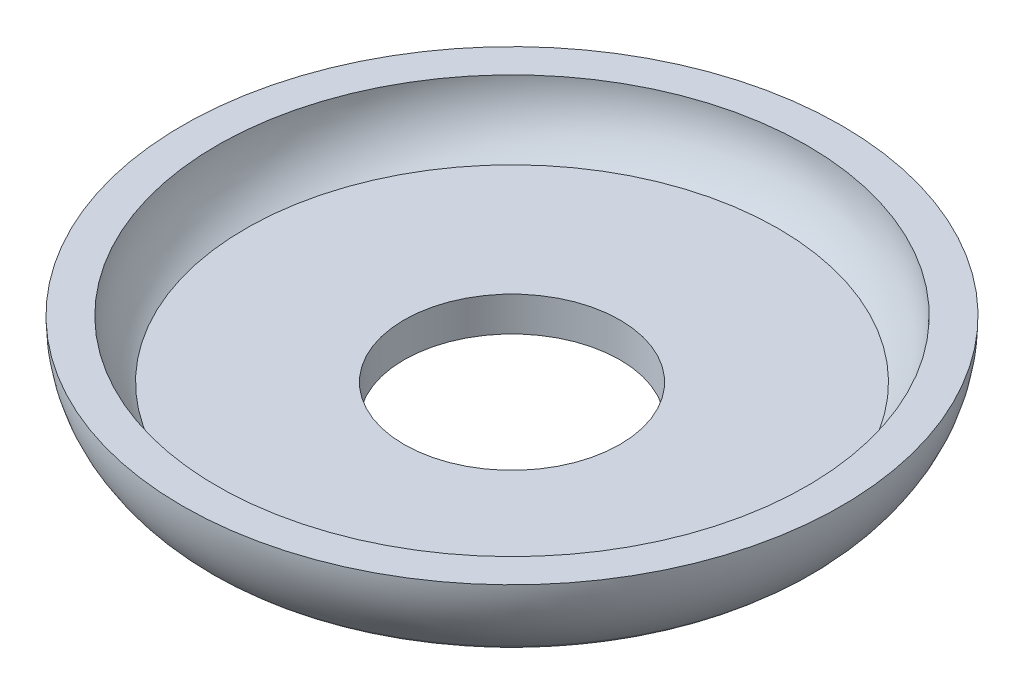
SolidWorks part; units mm, degrees
material "Cast Carbon Steel"
ref_plane "Front" through (0, 0, 0) normal (0, 0, 1) x (1, 0, 0)
ref_plane "Top" through (0, 0, 0) normal (0, 1, 0) x (1, 0, 0)
ref_plane "Right" through (0, 0, 0) normal (1, 0, 0) x (0, 0, -1)
sketch "Sketch2" plane through (0, 0, 0) normal (0, 0, 1) x (1, 0, 0)
  line L0 (4.7625, 0) -> (11.3718, 0)
  line L1 (14.5415, 4.064) -> (14.5415, 6.604) construction
  line L2 (4.7625, 1.524) -> (11.7475, 1.524)
  line L3 (4.7625, 1.524) -> (4.7625, 0)
  line L4 (13.0175, 4.064) -> (14.5415, 4.064)
  line L5 (4.7625, 0) -> (12.2014, 0) construction
  line L6 (0, 0) -> (0, 1.524) construction
  arc A0 (13.1709, 0.7471) -> (14.5415, 4.064) centre (9.8425, 4.064) ccw
  arc A1 (11.7475, 1.524) -> (13.0175, 4.064) centre (9.8425, 4.064) ccw
  arc A2 (12.2014, 0) -> (14.5415, 4.064) centre (9.8425, 4.064) ccw construction
  arc A3 (11.3718, 0) -> (13.1709, 0.7471) centre (11.3718, 2.54) ccw
  dimension "D1" = 4.7625
  dimension "D7" = 2.54
  dimension "D2" = 9.779
  dimension "D3" = 4.064
  dimension "D4" = 2.54
  dimension "D5" = 1.524
  dimension "D6" = 6.985
revolve "Revolve1" add sketch "Sketch2" angle 360 about L6
